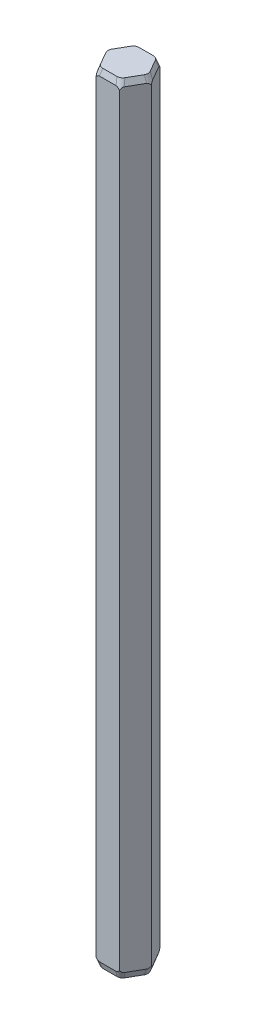
SolidWorks part; units mm, degrees
material "AISI 1020"
ref_plane "Front Plane" through (0, 0, 0) normal (0, 0, 1) x (1, 0, 0)
ref_plane "Top Plane" through (0, 0, 0) normal (0, 1, 0) x (1, 0, 0)
ref_plane "Right Plane" through (0, 0, 0) normal (1, 0, 0) x (0, 0, -1)
sketch "Sketch1" plane through (0, 0, 0) normal (0, 1, 0) x (1, 0, 0)
  line L1 (1.5, 0) -> (0.75, 1.299)
  line L2 (0.75, 1.299) -> (-0.75, 1.299)
  line L3 (-0.75, 1.299) -> (-1.5, 0)
  line L4 (-1.5, 0) -> (-0.75, -1.299)
  line L5 (-0.75, -1.299) -> (0.75, -1.299)
  line L6 (0.75, -1.299) -> (1.5, 0)
  circle A0 centre (0, 0) radius 1.299 construction
  circle A1 centre (0, 0) radius 1.5 construction
  dimension "D1" = 3
extrude "Boss-Extrude1" add sketch "Sketch1" along normal blind 50
chamfer "Chamfer1" distance 0.4 angle 19 12 edges at (1.125, 0, -0.6495) (0, 0, -1.299) (-1.125, 0, -0.6495) (-1.125, 0, 0.6495) (0, 0, 1.299) (1.125, 0, 0.6495) (0, 50, 1.299) (-1.125, 50, 0.6495) (-1.125, 50, -0.6495) (0, 50, -1.299) (1.125, 50, -0.6495) (1.125, 50, 0.6495)
fillet "Fillet1" radius 0.4 12 edges at (-0.7102, 0.2, -1.2302) (-1.4205, 0.2, 0) (-0.7102, 0.2, 1.2302) (0.7102, 0.2, -1.2302) (1.4205, 0.2, 0) (0.7102, 0.2, 1.2302) (-0.7102, 49.8, 1.2302) (-1.4205, 49.8, 0) (-0.7102, 49.8, -1.2302) (0.7102, 49.8, -1.2302) (1.4205, 49.8, 0) (0.7102, 49.8, 1.2302)
